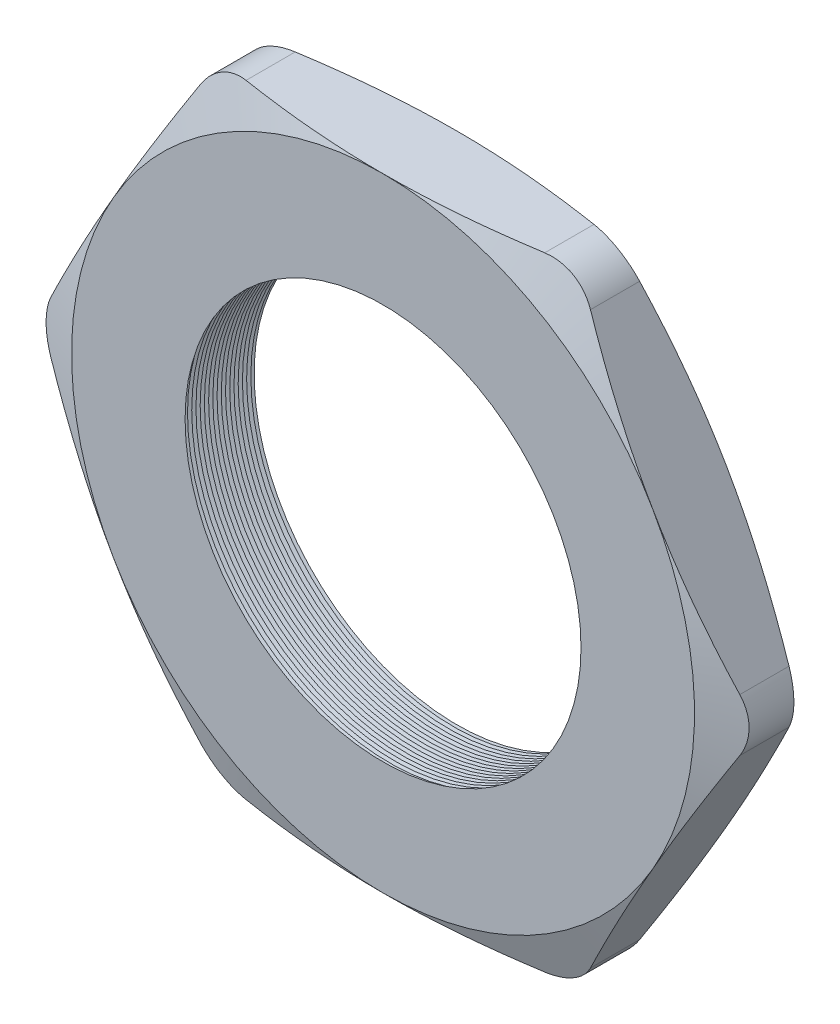
SolidWorks part; units mm, degrees
ref_plane "Front Plane" through (0, 0, 0) normal (0, 0, 1) x (1, 0, 0)
ref_plane "Top Plane" through (0, 0, 0) normal (0, 1, 0) x (1, 0, 0)
ref_plane "Right Plane" through (0, 0, 0) normal (1, 0, 0) x (0, 0, -1)
sketch "Sketch1" plane through (0, 0, 0) normal (0, 0, 1) x (1, 0, 0)
  line L1 (-17.3043, 0) -> (-8.6522, -14.986)
  line L2 (-8.6522, -14.986) -> (8.6522, -14.986)
  line L3 (8.6522, -14.986) -> (17.3043, 0)
  line L4 (17.3043, 0) -> (8.6522, 14.986)
  line L5 (8.6522, 14.986) -> (-8.6522, 14.986)
  line L6 (-8.6522, 14.986) -> (-17.3043, 0)
  circle A0 centre (0, 0) radius 14.986 construction
  circle A1 centre (0, 0) radius 9.525
  dimension "TS" = 19.05
  dimension "H" = 29.972
extrude "Extrude1" add sketch "Sketch1" along normal blind 3.556
fillet "Fillet1" radius 2.54 6 edges at (-8.6522, 14.986, 1.778) (-17.3043, 0, 1.778) (-8.6522, -14.986, 1.778) (8.6522, -14.986, 1.778) (17.3043, 0, 1.778) (8.6522, 14.986, 1.778)
sketch "Sketch2" plane through (0, 0, 3.556) normal (0, 0, 1) x (1, 0, 0)
  line L0 (7.1857, 14.986) -> (-7.1857, 14.986) construction
  circle A0 centre (0, 0) radius 14.986
extrude "Cut-Extrude1" cut sketch "Sketch2" against normal through all draft 70 flip side to cut
sketch "Sketch3" plane through (0, 0, 0) normal (0, 0, -1) x (-1, 0, 0)
  circle A0 centre (0, 0) radius 14.986
extrude "Cut-Extrude2" cut sketch "Sketch3" against normal through all draft 70 flip side to cut
sketch "Sketch4" plane through (0, 0, 0) normal (0, 1, 0) x (1, 0, 0)
  line L0 (-9.525, -3.556) -> (-9.525, -3.1161)
  line L2 (-9.525, -3.1161) -> (-9.906, -3.336)
  line L3 (-9.906, -3.336) -> (-9.525, -3.556)
  line L5 (-9.525, 0) -> (-9.525, -3.556) construction
  line L6 (-9.525, -3.556) -> (9.525, -3.556) construction
  dimension "D1" = 60
  dimension "D2" = 60
  dimension "D3" = 0.381
revolve "Cut-Revolve1" cut sketch "Sketch4" angle 360 about axis through (0, 0, 3.556) along (0, 0, -1)
pattern_linear "LPattern1" count 18 spacing 0.2032 along (0, 0, -1) of "Cut-Revolve1"
